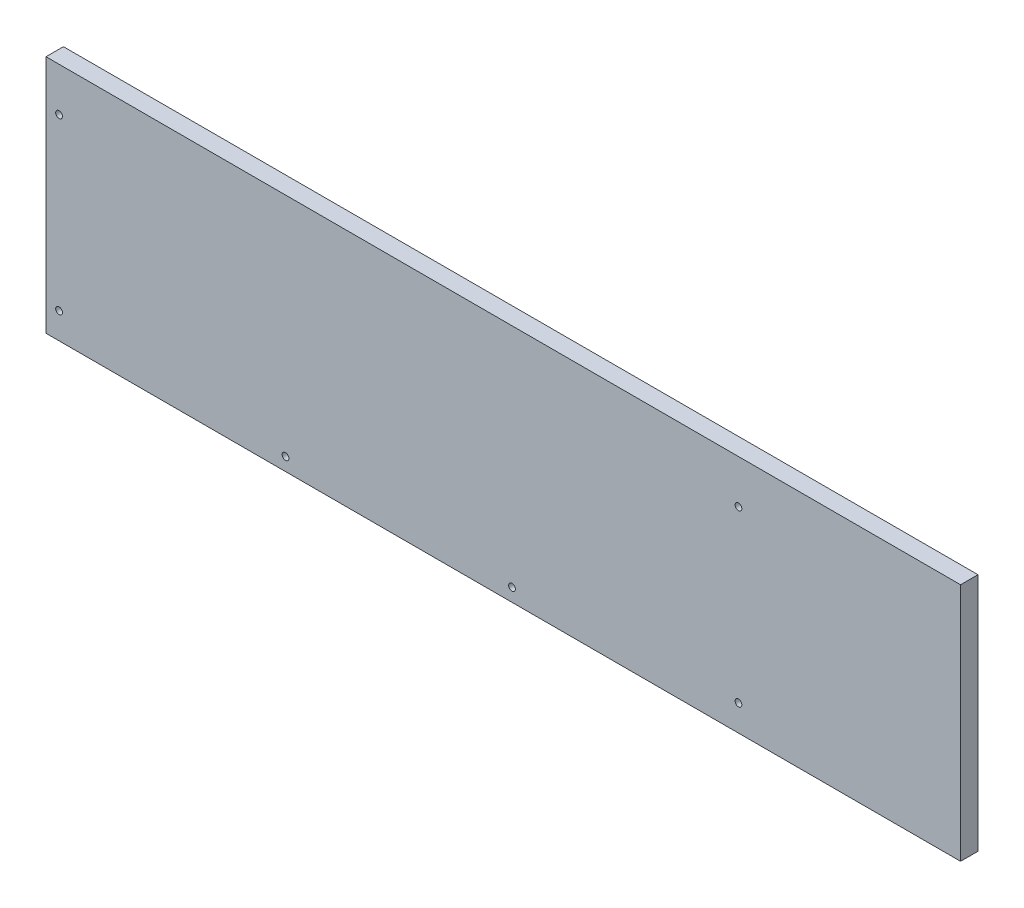
SolidWorks part; units mm, degrees
ref_plane "Front Plane" through (0, 0, 0) normal (0, 0, 1) x (1, 0, 0)
ref_plane "Top Plane" through (0, 0, 0) normal (0, 1, 0) x (1, 0, 0)
ref_plane "Right Plane" through (0, 0, 0) normal (1, 0, 0) x (0, 0, -1)
sketch "Sketch1" plane through (0, 0, 0) normal (0, 0, 1) x (1, 0, 0)
  line L1 (-210, 55) -> (210, 55)
  line L2 (-210, 55) -> (-210, -55)
  line L3 (-210, -55) -> (210, -55)
  line L4 (210, 55) -> (210, -55)
  line L5 (-210, 55) -> (210, -55) construction
  line L6 (-210, -55) -> (210, 55) construction
  point P0 (0, 0)
  dimension "D1" = 420
  dimension "D2" = 110
extrude "Boss-Extrude1" add sketch "Sketch1" along normal blind 8
sketch "Sketch2" plane through (0, 0, 0) normal (0, 0, 1) x (1, 0, 0)
  line L0 (-210, 55) -> (-210, -55) construction
  line L1 (210, 55) -> (-210, 55) construction
  line L2 (-210, -55) -> (210, -55) construction
  circle A0 centre (-204, 35) radius 1.55
  circle A1 centre (-204, -43) radius 1.55
  circle A2 centre (-100, -49) radius 1.55
  circle A3 centre (4, -49) radius 1.55
  circle A4 centre (108, -43) radius 1.55
  circle A5 centre (108, 35) radius 1.55
  dimension "D1" = 3.1
  dimension "D2" = 3.1
  dimension "D3" = 3.1
  dimension "D4" = 3.1
  dimension "D5" = 3.1
  dimension "D6" = 3.1
  dimension "D7" = 6
  dimension "D8" = 20
  dimension "D9" = 12
  dimension "D10" = 6
  dimension "D11" = 318
  dimension "D12" = 20
  dimension "D13" = 318
  dimension "D14" = 12
  dimension "D15" = 110
  dimension "D16" = 104
  dimension "D17" = 6
  dimension "D18" = 6
extrude "Cut-Extrude4" cut sketch "Sketch2" along normal through all
